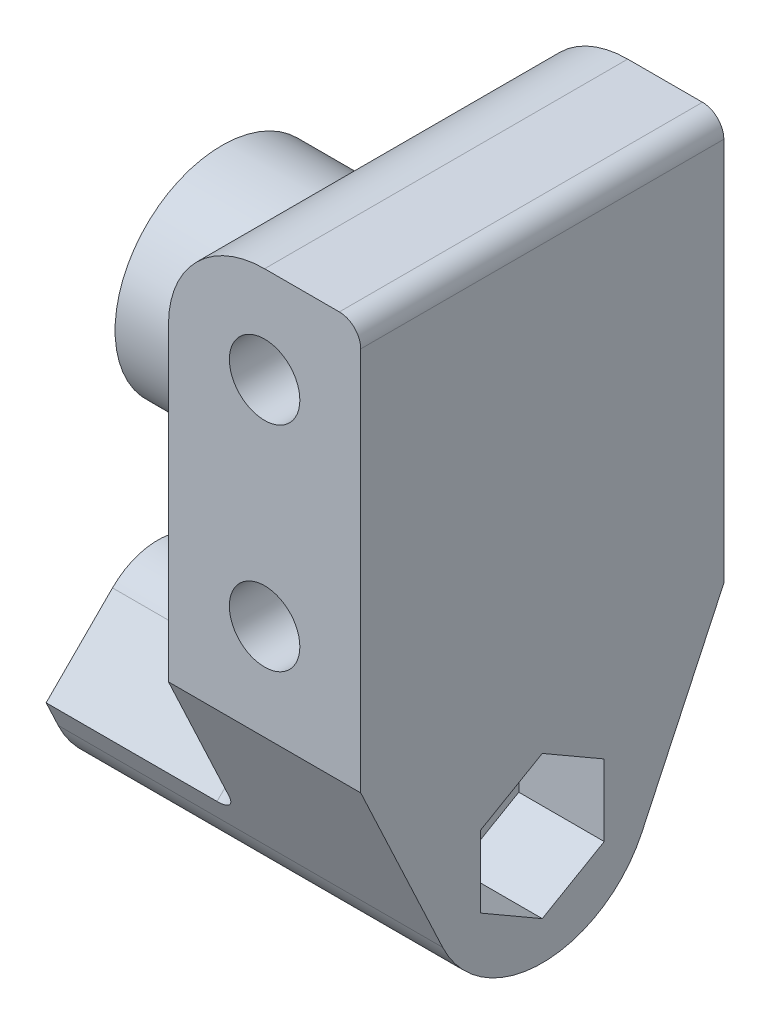
SolidWorks part; units mm, degrees
ref_plane "Front Plane" through (0, 0, 0) normal (0, 0, 1) x (1, 0, 0)
ref_plane "Top Plane" through (0, 0, 0) normal (0, 1, 0) x (1, 0, 0)
ref_plane "Right Plane" through (0, 0, 0) normal (1, 0, 0) x (0, 0, -1)
sketch "Sketch2" plane through (0, 0, 0) normal (0, 0, 1) x (1, 0, 0)
  line L0 (0, 0) -> (0, 10) construction
  line L1 (-4.5, 0) -> (-4.5, 10)
  line L2 (4.5, -4.5) -> (4.5, 14.5)
  line L3 (0, 14.5) -> (4.5, 14.5)
  line L4 (0, -4.5) -> (4.5, -4.5)
  arc A0 (-4.5, 0) -> (0, -4.5) centre (0, 0) ccw
  arc A1 (0, 14.5) -> (-4.5, 10) centre (0, 10) ccw
  circle A2 centre (0, 10) radius 1.65
  circle A3 centre (0, 0) radius 1.65
  point P3 (0, 5)
  dimension "D1" = 4.5
  dimension "D3" = 3.3
  dimension "D2" = 10
extrude "Boss-Extrude1" add sketch "Sketch2" along normal blind 17
sketch "Sketch3" plane through (4.5, 0, 0) normal (1, 0, 0) x (0, 0, -1)
  line L0 (-17, 5) -> (0, 5) construction
  line L1 (-17, -4.5) -> (-17, 14.5) construction
  line L2 (0, -4.5) -> (0, 14.5) construction
  line L3 (-8.5, 5) -> (-8.5, -10.5) construction
  line L4 (-13.1632, -12.6857) -> (-17, -4.5)
  line L5 (-17, -4.5) -> (0, -4.5)
  line L6 (0, -4.5) -> (-3.8368, -12.6857)
  circle A0 centre (-8.5, -10.5) radius 1.65
  arc A1 (-13.1632, -12.6857) -> (-3.8368, -12.6857) centre (-8.5, -10.5) ccw
  dimension "D2" = 3.3
  dimension "D3" = 3.5
  dimension "D1" = 15.5
extrude "Boss-Extrude2" add sketch "Sketch3" against normal up to vertex (13.2051 mm away)
sketch "Sketch4" plane through (0, -4.5, 0) normal (0, 1, 0) x (1, 0, 0)
  line L4 (0, -17) -> (0, 0)
  line L5 (0, 0) -> (-4.5, 0)
  line L6 (-4.5, 0) -> (-4.5, -17)
  line L7 (-4.5, -17) -> (0, -17)
  line L9 (0, 0) -> (-4.5, 0)
  line L10 (-4.5, 0) -> (-4.5, -17)
  line L11 (-4.5, -17) -> (0, -17)
  line L12 (0, -17) -> (0, 0)
  dimension "D1" = 0
extrude "Boss-Extrude4" add sketch "Sketch4" along normal up to surface (4.5 mm away)
sketch "Sketch8" plane through (-4.5, 0, 0) normal (-1, 0, 0) x (0, 0, 1)
  line L1 (8.5, -7.1514) -> (5.6, -8.8257)
  line L2 (5.6, -8.8257) -> (5.6, -12.1743)
  line L3 (5.6, -12.1743) -> (8.5, -13.8486)
  line L4 (8.5, -13.8486) -> (11.4, -12.1743)
  line L5 (11.4, -12.1743) -> (11.4, -8.8257)
  line L6 (11.4, -8.8257) -> (8.5, -7.1514)
  circle A0 centre (8.5, -10.5) radius 2.9 construction
  dimension "D1" = 5.8
extrude "Cut-Extrude2" cut sketch "Sketch8" against normal blind 13 from offset 5 offset against normal yes
sketch "Sketch11" plane through (-4.5, 0, 0) normal (1, 0, 0) x (0, 0, -1)
  line L0 (-17, 5) -> (0, 5) construction
  line L3 (-17, 10) -> (0, 10) construction
  line L4 (0, -4.5) -> (0, 14.5) construction
  line L5 (-17, -4.5) -> (-17, 14.5) construction
  circle A0 centre (-8.5, 5) radius 5
  dimension "D1" = 10
  dimension "D2" = 5
extrude "Boss-Extrude5" add sketch "Sketch11" against normal blind 6
fillet "Fillet1" radius 1 1 edges at (-4.5, 5, 3.5)
fillet "Fillet2" radius 1 1 edges at (4.5, 14.5, 8.5)
sketch "Sketch12" plane through (-4.5, 0, 0) normal (-1, 0, 0) x (0, 0, 1)
  line L3 (13.1632, -12.6857) -> (13.7265, -11.4839)
  line L4 (17, -4.5) -> (13.1632, -12.6857) construction
  line L5 (13.7265, -11.4839) -> (10.6213, -8.3787)
  line L6 (6.3787, -8.3787) -> (3.2735, -11.4839)
  line L7 (3.8368, -12.6857) -> (0, -4.5) construction
  line L8 (3.2735, -11.4839) -> (3.8368, -12.6857)
  line L9 (8.5, -10.5) -> (8.5, -7.5) construction
  arc A0 (10.6213, -8.3787) -> (6.3787, -8.3787) centre (8.5, -10.5) ccw
  arc A1 (3.8368, -12.6857) -> (13.1632, -12.6857) centre (8.5, -10.5) ccw construction
  arc A2 (3.8368, -12.6857) -> (13.1632, -12.6857) centre (8.5, -10.5) ccw
  circle A3 centre (8.5, -10.5) radius 1.65 construction
  circle A4 centre (8.5, -10.5) radius 1.65
  dimension "D1" = 6
extrude "Boss-Extrude6" add sketch "Sketch12" along normal blind 9
fillet "Fillet3" radius 1 3 edges at (-4.5, -9.9313, 12.1739) (-4.5, -9.9313, 4.8261) (-4.5, -7.5, 8.5)
